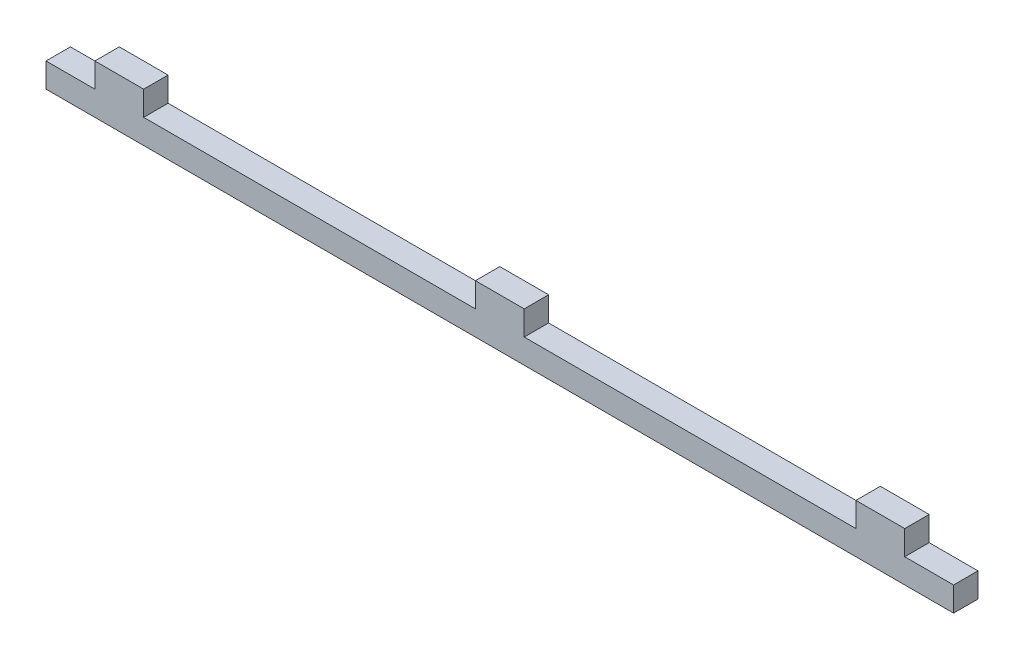
SolidWorks part; units mm, degrees
ref_plane "Front Plane" through (0, 0, 0) normal (0, 0, 1) x (1, 0, 0)
ref_plane "Top Plane" through (0, 0, 0) normal (0, 1, 0) x (1, 0, 0)
ref_plane "Right Plane" through (0, 0, 0) normal (1, 0, 0) x (0, 0, -1)
sketch "Sketch2" plane through (0, 0, 0) normal (0, 1, 0) x (1, 0, 0)
  line L0 (0, 0) -> (0, 6) construction
  dimension "D1" = 6
sketch "Sketch1" plane through (0, 0, 0) normal (0, 0, 1) x (1, 0, 0)
  line L0 (0, 0) -> (0, 9) construction
  line L1 (-111.5, -3) -> (111.5, -3)
  line L2 (-111.5, -3) -> (-111.5, 3)
  line L3 (-111.5, 3) -> (111.5, 3)
  line L4 (111.5, -3) -> (111.5, 3)
  line L5 (-111.5, -3) -> (111.5, 3) construction
  line L6 (-111.5, 3) -> (111.5, -3) construction
  line L7 (-99.5, 3) -> (-87.5, 3)
  line L8 (-99.5, 3) -> (-99.5, 9)
  line L9 (-99.5, 9) -> (-87.5, 9)
  line L10 (-87.5, 3) -> (-87.5, 9)
  line L11 (-6, 3) -> (6, 3)
  line L12 (-6, 3) -> (-6, 9)
  line L13 (-6, 9) -> (6, 9)
  line L14 (6, 3) -> (6, 9)
  line L15 (87.5, 3) -> (99.5, 3)
  line L16 (87.5, 3) -> (87.5, 9)
  line L17 (87.5, 9) -> (99.5, 9)
  line L18 (99.5, 3) -> (99.5, 9)
  line L19 (-87.5, 9) -> (-6, 9) construction
  line L20 (6, 9) -> (87.5, 9) construction
  point P0 (0, 0)
  dimension "D1" = 6
  dimension "D2" = 223
  dimension "D3" = 12
  dimension "D4" = 12
extrude "Boss-Extrude1" add sketch "Sketch1" against normal up to vertex (6 mm away) contours L3 L10 L9 L8 | L1 L4 L3 L2 | L3 L14 L13 L12 | L3 L18 L17 L16 up to point (0, 0, -6)
equation "\"t_wood\"= 6' Thickness of the wood"
equation "\"t_glass\"= 2.5'Thickness of glass panels"
equation "\"w_glass\"= 248"
equation "\"h_glass\"= 167"
equation "\"h_food_internal\" = 60"
equation "\"entry_height\"= 20"
equation "\"entry diameter\"= 8"
equation "\"glass_bottom_overlap\"= 8"
equation "\"default_finger_size\"= 12"
equation "\"brood_depth\"= 42"
equation "\"outer_box_depth\" = \"brood_depth\" + ( 2 * \"t_glass\" ) + ( 2 * \"t_wood\" )"
equation "\"outer_box_width\"= \"w_glass\" + ( 2 * \"t_wood\" )"
equation "\"food_top_clearance\"= 10"
equation "\"outer_box_height\"= \"t_wood\" + \"h_glass\" + \"t_wood\" + \"h_food_internal\" + \"food_top_clearance\" + \"t_wood\""
equation "\"food_internal_depth\"= \"brood_depth\" + \"t_glass\" + \"t_glass\" - \"t_wood\" - \"t_wood\""
equation "\"food_channel_clearance_width\"= 14"
equation "\"bar_top_play\"= 4.5"
equation "\"bar_entry_angle\"= 10"
equation "\"bar_width\"= 20"
equation "\"entry_disk_play\"= 0.3"
equation "\"D1@Sketch2\"=\"t_wood\""
equation "\"D1@Sketch1\"=\"t_wood\""
equation "\"D2@Sketch1\"=\"w_glass\"-( \"t_wood\" *4)-1"
equation "\"D3@Sketch1\"=\"t_wood\"*2"
equation "\"D4@Sketch1\"=\"default_finger_size\""
